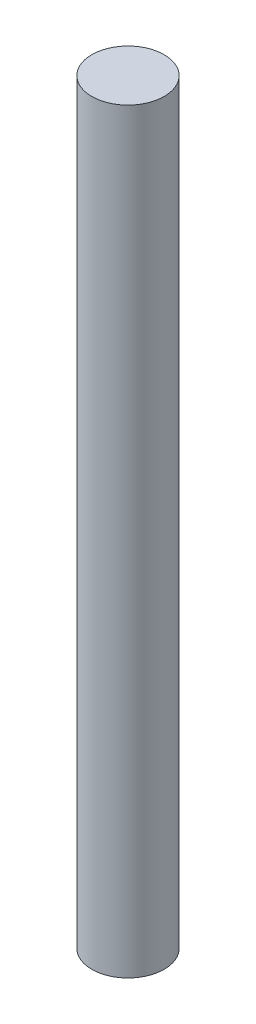
SolidWorks part; units mm, degrees
ref_plane "Front Plane" through (0, 0, 0) normal (0, 0, 1) x (1, 0, 0)
ref_plane "Top Plane" through (0, 0, 0) normal (0, 1, 0) x (1, 0, 0)
ref_plane "Right Plane" through (0, 0, 0) normal (1, 0, 0) x (0, 0, -1)
sketch "Sketch1" plane through (0, 0, 0) normal (0, 1, 0) x (1, 0, 0)
  circle A0 centre (0, 0) radius 2.5
  dimension "D1" = 5
extrude "Boss-Extrude1" add sketch "Sketch1" along normal blind 52.2
